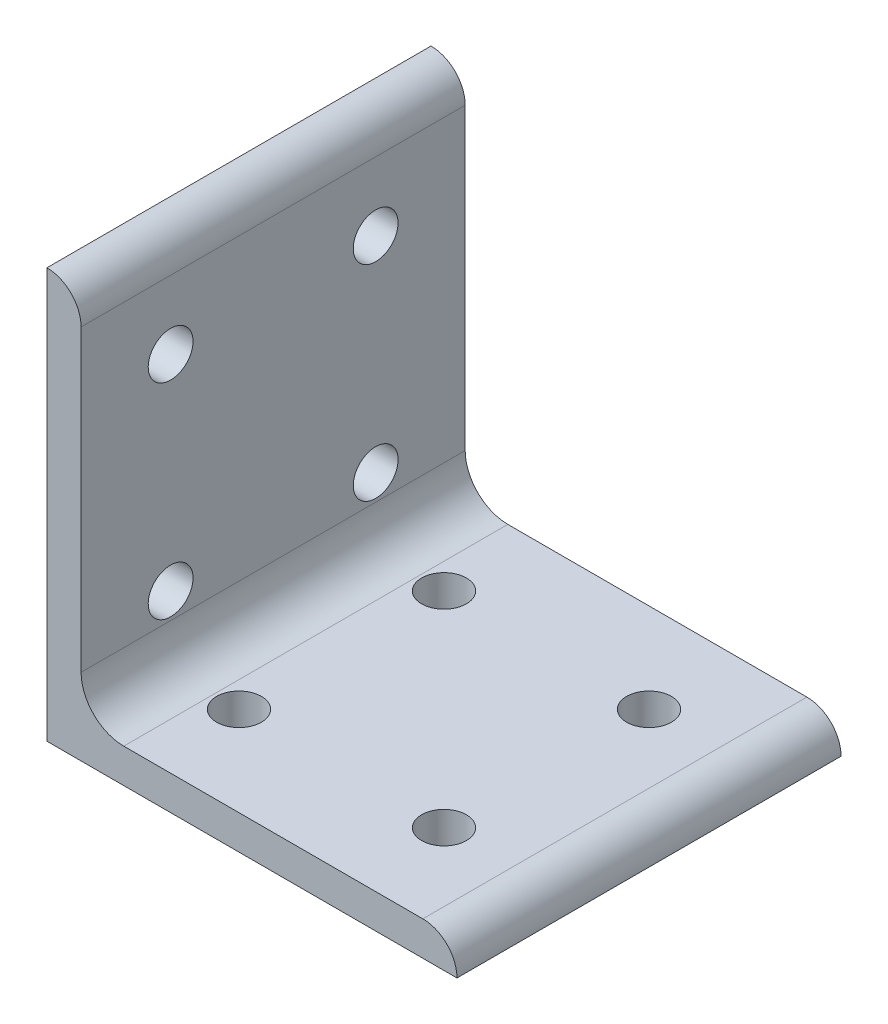
SolidWorks part; units mm, degrees
ref_plane "Front Plane" through (0, 0, 0) normal (0, 0, 1) x (1, 0, 0)
ref_plane "Top Plane" through (0, 0, 0) normal (0, 1, 0) x (1, 0, 0)
ref_plane "Right Plane" through (0, 0, 0) normal (1, 0, 0) x (0, 0, -1)
sketch "Sketch1" plane through (0, 0, 0) normal (0, 0, 1) x (1, 0, 0)
  line L0 (0, 0) -> (0, 76.2)
  line L1 (6.35, 69.85) -> (6.35, 76.2) construction
  line L2 (6.35, 69.85) -> (6.35, 14.2748)
  line L3 (14.2748, 6.35) -> (69.85, 6.35)
  line L4 (6.35, 76.2) -> (0, 76.2) construction
  line L5 (76.2, 0) -> (0, 0)
  line L6 (69.85, 6.35) -> (76.2, 6.35) construction
  line L7 (76.2, 6.35) -> (76.2, 0) construction
  arc A0 (6.35, 69.85) -> (0, 76.2) centre (0, 69.85) ccw
  arc A1 (76.2, 0) -> (69.85, 6.35) centre (69.85, 0) ccw
  arc A2 (6.35, 14.2748) -> (14.2748, 6.35) centre (14.2748, 14.2748) ccw
  point P10 (6.35, 73.025)
  dimension "E" = 7.9248
  dimension "D" = 6.35
  dimension "C" = 76.2
  dimension "B" = 76.2
extrude "Boss-Extrude1" add sketch "Sketch1" along normal mid plane 71.374
sketch "Sketch2" plane through (0, 0, 0) normal (0, 1, 0) x (1, 0, 0)
  line L0 (0, -19.05) -> (19.05, -19.05) construction
  line L1 (19.05, -19.05) -> (57.15, -19.05) construction
  line L2 (0, -19.05) -> (0, 19.05) construction
  line L3 (0, 19.05) -> (19.05, 19.05) construction
  line L4 (57.15, 19.05) -> (57.15, -19.05) construction
  line L5 (0, -19.05) -> (0, -35.687) construction
  line L6 (19.05, -19.05) -> (19.05, 19.05) construction
  line L7 (19.05, 19.05) -> (57.15, 19.05) construction
  circle A0 centre (19.05, -19.05) radius 4.1656
  circle A1 centre (57.15, -19.05) radius 4.1656
  circle A2 centre (19.05, 19.05) radius 4.1656
  circle A3 centre (57.15, 19.05) radius 4.1656
extrude "Cut-Extrude1" cut sketch "Sketch2" along normal through all
sketch "Sketch3" plane through (0, 0, 0) normal (1, 0, 0) x (0, 0, -1)
  line L0 (-19.05, 0) -> (-19.05, 19.05) construction
  line L1 (-19.05, 19.05) -> (-19.05, 57.15) construction
  line L2 (19.05, 0) -> (19.05, 19.05) construction
  line L3 (19.05, 19.05) -> (-19.05, 19.05) construction
  line L4 (19.05, 19.05) -> (19.05, 57.15) construction
  line L5 (19.05, 57.15) -> (-19.05, 57.15) construction
  circle A0 centre (-19.05, 19.05) radius 4.1656
  circle A1 centre (-19.05, 57.15) radius 4.1656
  circle A2 centre (19.05, 19.05) radius 4.1656
  circle A3 centre (19.05, 57.15) radius 4.1656
  dimension "D1" = 19.05
  dimension "D2" = 38.1
extrude "Cut-Extrude2" cut sketch "Sketch3" along normal through all
equation "\"E@Sketch3\" = \"E@Sketch2\""
equation "\"D1@Sketch3\" = \"D1@Sketch2\""
equation "\"D2@Sketch3\" = \"D2@Sketch2\""
